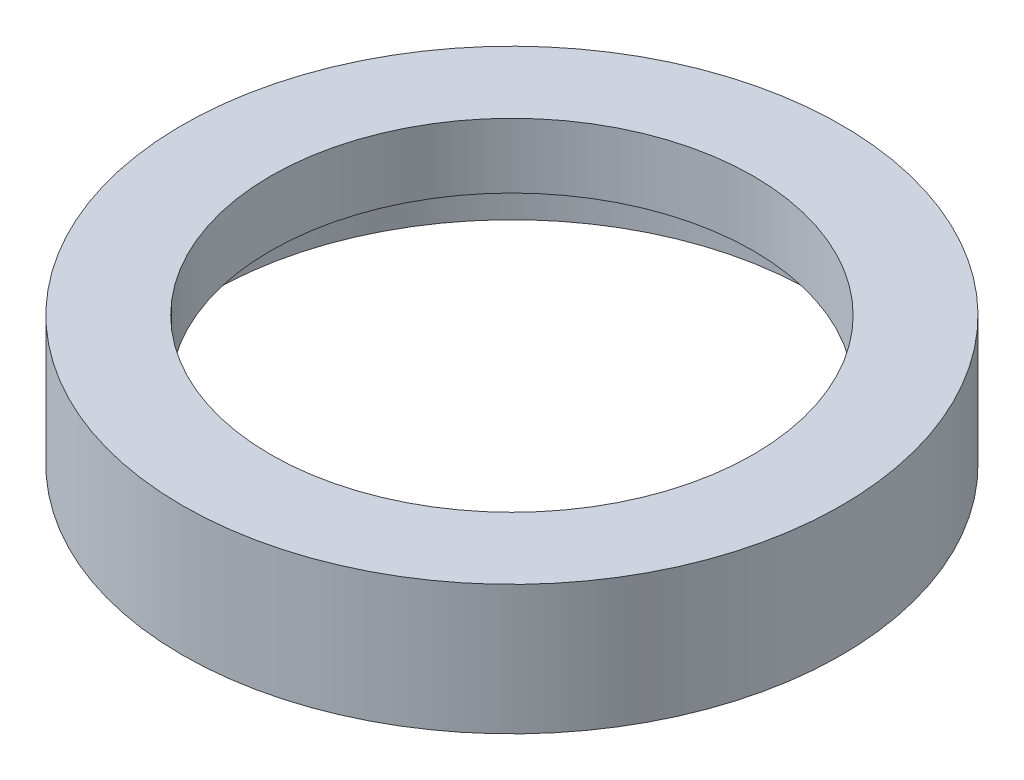
SolidWorks part; units mm, degrees
ref_plane "前视基准面" through (0, 0, 0) normal (0, 0, 1) x (1, 0, 0)
ref_plane "上视基准面" through (0, 0, 0) normal (0, 1, 0) x (1, 0, 0)
ref_plane "右视基准面" through (0, 0, 0) normal (1, 0, 0) x (0, 0, -1)
sketch "草图1" plane through (0, 0, 0) normal (0, 0, 1) x (1, 0, 0)
  line L0 (0, 60.0208) -> (0, -56.4315) construction
  line L1 (25.5, 0) -> (25.5, 4.5)
  line L2 (25.5, 4.5) -> (26.1, 4.5)
  line L3 (26.1, 4.5) -> (26.1, 5.5)
  line L4 (26.1, 5.5) -> (20.5, 5.5)
  line L5 (20.5, 5.5) -> (20.5, 11)
  line L6 (20.5, 11) -> (28, 11)
  line L7 (28, 11) -> (28, 0)
  line L8 (28, 0) -> (25.5, 0)
  point P5 (23.3, 5.5)
  dimension "D1" = 28
  dimension "D2" = 20.5
  dimension "D3" = 26.1
  dimension "D4" = 25.5
  dimension "D5" = 1
  dimension "D6" = 5.5
  dimension "D7" = 11
revolve "旋转1" add sketch "草图1" angle 360 about L0
cosmetic thread "装饰螺纹线1" parameters "D2"=42
cosmetic thread "装饰螺纹线2" parameters "D2"=52
